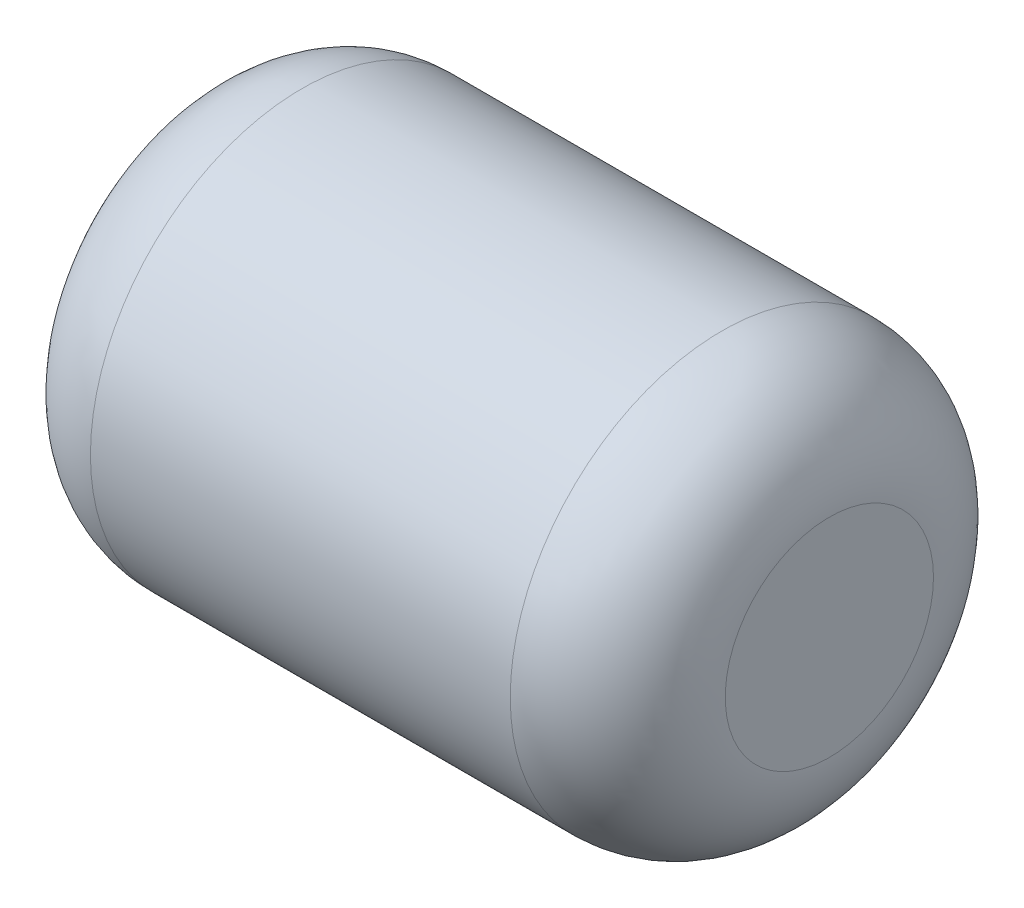
SolidWorks part; units mm, degrees
material "SmCo 26 (17:2)"
ref_plane "Front" through (0, 0, 0) normal (0, 0, 1) x (1, 0, 0)
ref_plane "Top" through (0, 0, 0) normal (0, 1, 0) x (1, 0, 0)
ref_plane "Right" through (0, 0, 0) normal (1, 0, 0) x (0, 0, -1)
sketch "Sketch1" plane through (0, 0, 0) normal (1, 0, 0) x (0, 0, -1)
  circle A0 centre (0, 0) radius 1
  dimension "D1" = 2
extrude "Extrude1" add sketch "Sketch1" along normal blind 3
fillet "Fillet1" radius 0.508 2 edges at (0, 0, -1) (3, 0, -1)
